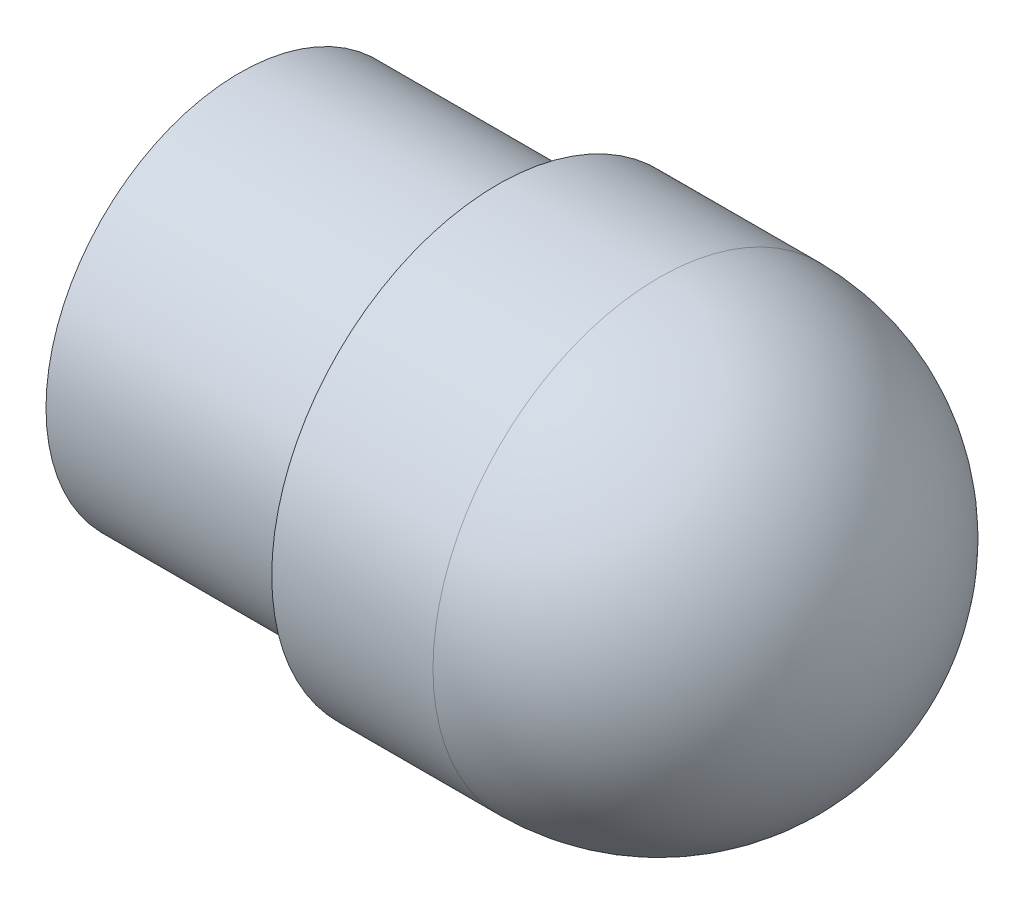
SolidWorks part; units mm, degrees
ref_plane "Alzado" through (0, 0, 0) normal (0, 0, 1) x (1, 0, 0)
ref_plane "Planta" through (0, 0, 0) normal (0, 1, 0) x (1, 0, 0)
ref_plane "Vista lateral" through (0, 0, 0) normal (1, 0, 0) x (0, 0, -1)
sketch "Croquis1" plane through (0, 0, 0) normal (0, 0, 1) x (1, 0, 0)
  line L5 (0, 0) -> (50, 0)
  line L6 (0, 0) -> (0, 15)
  line L7 (0, 15) -> (20, 15)
  line L8 (20, 15) -> (20, 17.5)
  line L9 (20, 17.5) -> (32.5, 17.5)
  circle A1 centre (-105.9969, 77.9837) radius 17.5
  arc A2 (32.5, 17.5) -> (50, 0) centre (32.5, 0) cw
  dimension "D2" = 15
  dimension "D4" = 35
  dimension "D1" = 50
  dimension "D3" = 20
  dimension "D5" = 2.5
  dimension "D6" = 12.5
revolve "Revolución1" add sketch "Croquis1" angle 360 about L5
